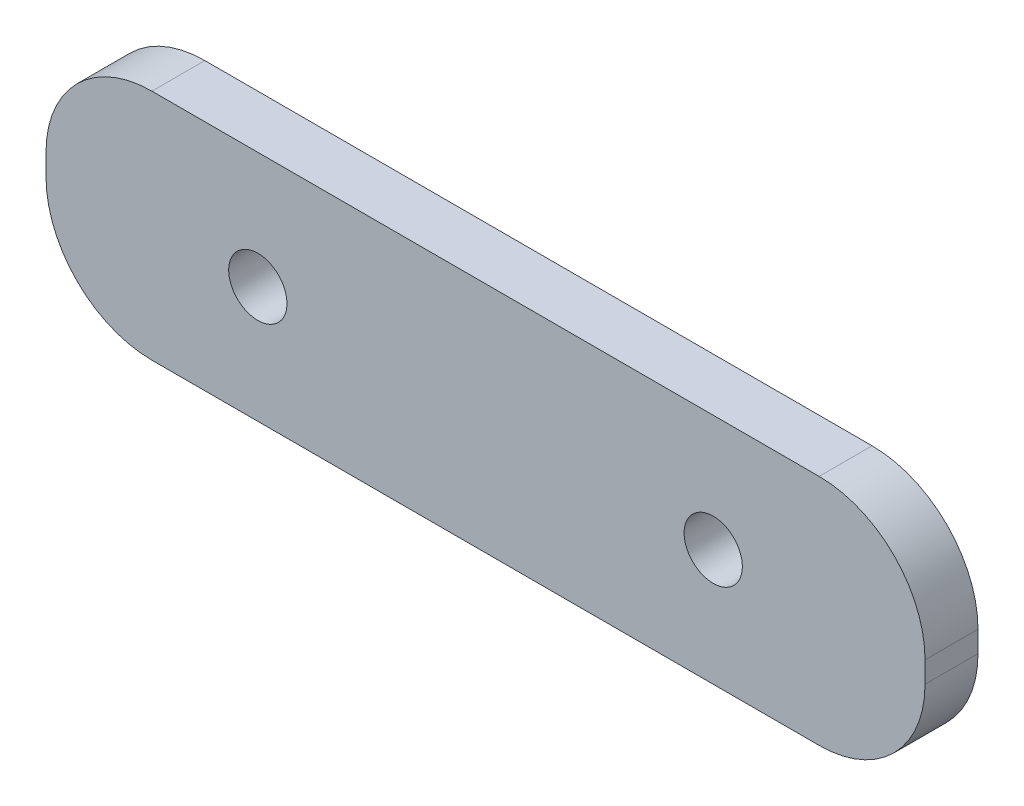
SolidWorks part; units mm, degrees
ref_plane "Front Plane" through (0, 0, 0) normal (0, 0, 1) x (1, 0, 0)
ref_plane "Top Plane" through (0, 0, 0) normal (0, 1, 0) x (1, 0, 0)
ref_plane "Right Plane" through (0, 0, 0) normal (1, 0, 0) x (0, 0, -1)
sketch "Sketch1" plane through (0, 0, 0) normal (0, 0, 1) x (1, 0, 0)
  line L0 (0, 0) -> (0, -22.5) construction
  line L1 (-41.5, -33.5) -> (41.5, -33.5)
  line L2 (-41.5, -33.5) -> (-41.5, 33.5)
  line L3 (-41.5, 33.5) -> (41.5, 33.5)
  line L4 (41.5, -33.5) -> (41.5, 33.5)
  line L5 (-41.5, -33.5) -> (41.5, 33.5) construction
  line L6 (-41.5, 33.5) -> (41.5, -33.5) construction
  line L7 (0, -22.5) -> (21.5, -22.5) construction
  point P0 (0, 0)
  dimension "D1" = 21.5
  dimension "D2" = 11
  dimension "D3" = 83
  dimension "D4" = 67
extrude "Boss-Extrude1" add sketch "Sketch1" along normal blind 5
hole_wizard "M5 Clearance Hole1" positions "Sketch2" profile "Sketch3" hole size "M5" standard "ISO" end condition through all
sketch "Sketch2" plane through (0, 0, 5) normal (0, 0, 1) x (1, 0, 0)
  line L0 (-21.5, -22.5) -> (21.5, -22.5) construction
  line L2 (0, -22.5) -> (0, 0) construction
  line L4 (-41.5, -33.5) -> (41.5, -33.5) construction
  point P0 (21.5, -22.5)
  point P3 (-21.5, -22.5)
  dimension "D1" = 43
  dimension "D2" = 11
sketch "Sketch3" plane through (21.5, -22.5, 5) normal (1, 0, 0) x (0, -1, 0)
  line L0 (0, 0) -> (0, 5)
  line L1 (0, 5) -> (2.75, 5)
  line L2 (2.75, 5) -> (2.75, 0)
  line L5 (2.75, 0) -> (0, 0)
  line L11 (0, -6.35) -> (0, 107.95) construction
  dimension "Thru Hole Dia." = 5.5
  dimension "Thru Hole Depth" = 5
hole_wizard "M3 Clearance Hole1" positions "Sketch4" profile "Sketch5" hole size "M3" standard "ISO" end condition through all
sketch "Sketch4" plane through (0, 0, 0) normal (0, 0, -1) x (-1, 0, 0)
  circle A0 centre (-1.0411, -3) radius 1.5 construction
  point P0 (-32.0411, 28)
  point P3 (-1.0411, 28)
  point P6 (-1.0411, -3)
  point P8 (-32.0411, -3)
sketch "Sketch5" plane through (32.0411, 28, 0) normal (1, 0, 0) x (0, 1, 0)
  line L0 (0, 0) -> (0, 5)
  line L1 (0, 5) -> (1.7, 5)
  line L2 (1.7, 5) -> (1.7, 0)
  line L5 (1.7, 0) -> (0, 0)
  line L11 (0, -6.35) -> (0, 107.95) construction
  dimension "Thru Hole Dia." = 3.4
  dimension "Thru Hole Depth" = 5
sketch "Sketch6" plane through (0, 0, 5) normal (0, 0, 1) x (1, 0, 0)
  circle A0 centre (16.5411, 12.5) radius 11.05
  dimension "D1" = 22.1
extrude "Cut-Extrude1" cut sketch "Sketch6" against normal through all
fillet "Fillet1" radius 10 4 edges at (41.5, -33.5, 2.5) (-41.5, -33.5, 2.5) (-41.5, 33.5, 2.5) (41.5, 33.5, 2.5)
sketch "Sketch7" plane through (0, 0, 5) normal (0, 0, 1) x (1, 0, 0)
  line L0 (-21.5, -22.5) -> (-21.5, -33.5) construction
  line L1 (-45.5745, 36.9622) -> (51.3391, 36.9622)
  line L2 (-45.5745, 36.9622) -> (-45.5745, -11.5)
  line L3 (-45.5745, -11.5) -> (51.3391, -11.5)
  line L4 (51.3391, 36.9622) -> (51.3391, -11.5)
  line L5 (-31.5, -33.5) -> (31.5, -33.5) construction
  line L6 (-21.5, -22.5) -> (-21.5, -11.5) construction
extrude "Cut-Extrude2" cut sketch "Sketch7" against normal through all
fillet "Fillet2" radius 10 2 edges at (41.5, -11.5, 2.5) (-41.5, -11.5, 2.5)
